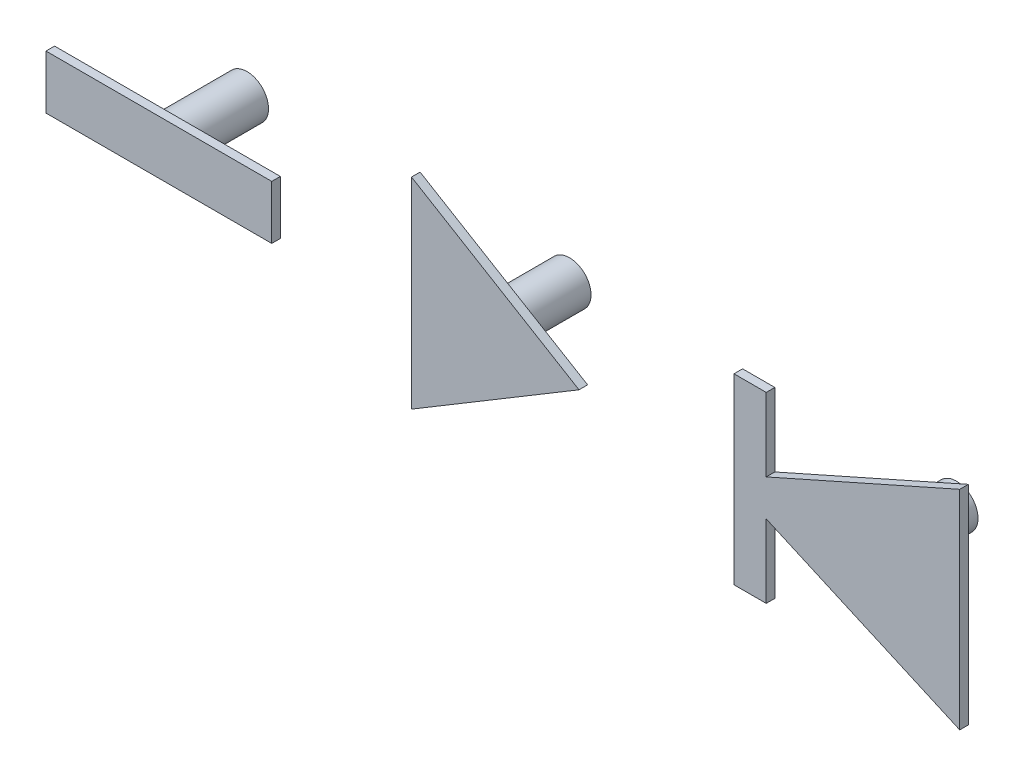
SolidWorks part; units mm, degrees
ref_plane "Front Plane" through (0, 0, 0) normal (0, 0, 1) x (1, 0, 0)
ref_plane "Top Plane" through (0, 0, 0) normal (0, 1, 0) x (1, 0, 0)
ref_plane "Right Plane" through (0, 0, 0) normal (1, 0, 0) x (0, 0, -1)
sketch "Sketch2" plane through (0, 0, 0) normal (0, 0, 1) x (1, 0, 0)
  line L0 (-5, 5.1169) -> (-5, -5.1169)
  line L1 (-4.2428, -5.5457) -> (4.2854, -0.4287)
  line L2 (4.2854, 0.4287) -> (-4.2428, 5.5457)
  line L3 (10, 4.5) -> (10, -4.5)
  line L4 (10.5, -5) -> (12.5, -5)
  line L5 (13, -4.5) -> (13, -2)
  line L6 (13, -2) -> (21.2969, -5.6875)
  line L7 (22, -5.2306) -> (22, 5.2306)
  line L8 (21.2969, 5.6875) -> (13, 2)
  line L9 (13, 2) -> (13, 4.5)
  line L10 (12.5, 5) -> (10.5, 5)
  line L12 (-21.5, 2) -> (-10.5, 2)
  line L13 (-22, 1.5) -> (-22, -1.5)
  line L14 (-21.5, -2) -> (-10.5, -2)
  line L15 (-10, 1.5) -> (-10, -1.5)
  arc A0 (21.2969, 5.6875) -> (22, 5.2306) centre (21.5, 5.2306) cw
  arc A1 (22, -5.2306) -> (21.2969, -5.6875) centre (21.5, -5.2306) cw
  arc A2 (12.5, -5) -> (13, -4.5) centre (12.5, -4.5) ccw
  arc A3 (10.5, -5) -> (10, -4.5) centre (10.5, -4.5) cw
  arc A4 (13, 4.5) -> (12.5, 5) centre (12.5, 4.5) ccw
  arc A5 (10, 4.5) -> (10.5, 5) centre (10.5, 4.5) cw
  arc A6 (4.2854, -0.4287) -> (4.2854, 0.4287) centre (4.0282, 0) ccw
  arc A7 (-4.2428, -5.5457) -> (-5, -5.1169) centre (-4.5, -5.1169) cw
  arc A8 (-4.2428, 5.5457) -> (-5, 5.1169) centre (-4.5, 5.1169) ccw
  arc A9 (-10.5, 2) -> (-10, 1.5) centre (-10.5, 1.5) cw
  arc A10 (-10.5, -2) -> (-10, -1.5) centre (-10.5, -1.5) ccw
  arc A11 (-22, -1.5) -> (-21.5, -2) centre (-21.5, -1.5) ccw
  arc A12 (-22, 1.5) -> (-21.5, 2) centre (-21.5, 1.5) cw
  dimension "D1" = 0.5
sketch "Sketch3" plane through (0, 0, 0) normal (0, 0, 1) x (1, 0, 0)
  line L1 (-24, 10) -> (25, 10)
  line L2 (-25, 9) -> (-25, -9)
  line L3 (-24, -10) -> (25, -10)
  line L4 (26, 9) -> (26, -9)
  arc A0 (25, 10) -> (26, 9) centre (25, 9) cw
  arc A1 (26, -9) -> (25, -10) centre (25, -9) cw
  arc A2 (-24, -10) -> (-25, -9) centre (-24, -9) cw
  arc A3 (-24, 10) -> (-25, 9) centre (-24, 9) ccw
  dimension "D1" = 1
ref_plane "Plane1" through (0, 0, 5) normal (0, 0, 1) x (1, 0, 0)
sketch "Sketch4" plane through (0, 0, 5) normal (0, 0, 1) x (1, 0, 0)
  line L0 (-5, 5.1169) -> (-5, -5.1169)
  line L1 (-4.2428, -5.5457) -> (4.2854, -0.4287)
  line L2 (4.2854, 0.4287) -> (-4.2428, 5.5457)
  line L3 (10, 4.5) -> (10, -4.5)
  line L4 (10.5, -5) -> (12.5, -5)
  line L5 (13, -4.5) -> (13, -2)
  line L6 (13, -2) -> (21.2969, -5.6875)
  line L7 (22, -5.2306) -> (22, 5.2306)
  line L8 (21.2969, 5.6875) -> (13, 2)
  line L9 (13, 2) -> (13, 4.5)
  line L10 (12.5, 5) -> (10.5, 5)
  line L12 (-21.5, 2) -> (-10.5, 2)
  line L13 (-22, 1.5) -> (-22, -1.5)
  line L14 (-21.5, -2) -> (-10.5, -2)
  line L15 (-10, 1.5) -> (-10, -1.5)
  arc A0 (21.2969, 5.6875) -> (22, 5.2306) centre (21.5, 5.2306) cw
  arc A1 (22, -5.2306) -> (21.2969, -5.6875) centre (21.5, -5.2306) cw
  arc A2 (12.5, -5) -> (13, -4.5) centre (12.5, -4.5) ccw
  arc A3 (10.5, -5) -> (10, -4.5) centre (10.5, -4.5) cw
  arc A4 (13, 4.5) -> (12.5, 5) centre (12.5, 4.5) ccw
  arc A5 (10, 4.5) -> (10.5, 5) centre (10.5, 4.5) cw
  arc A6 (4.2854, -0.4287) -> (4.2854, 0.4287) centre (4.0282, 0) ccw
  arc A7 (-4.2428, -5.5457) -> (-5, -5.1169) centre (-4.5, -5.1169) cw
  arc A8 (-4.2428, 5.5457) -> (-5, 5.1169) centre (-4.5, 5.1169) ccw
  arc A9 (-10.5, 2) -> (-10, 1.5) centre (-10.5, 1.5) cw
  arc A10 (-10.5, -2) -> (-10, -1.5) centre (-10.5, -1.5) ccw
  arc A11 (-22, -1.5) -> (-21.5, -2) centre (-21.5, -1.5) ccw
  arc A12 (-22, 1.5) -> (-21.5, 2) centre (-21.5, 1.5) cw
  dimension "D1" = 0.5
sketch "Sketch5" plane through (0, 0, 5) normal (0, 0, 1) x (1, 0, 0)
  line L0 (-4.25, 4.6754) -> (-4.25, -4.6754)
  line L1 (-4.25, -4.6754) -> (3.5423, 0)
  line L2 (3.5423, 0) -> (-4.25, 4.6754)
  line L3 (10.75, 4.25) -> (10.75, -4.25)
  line L4 (10.75, -4.25) -> (12.25, -4.25)
  line L5 (12.25, -4.25) -> (12.25, -0.8459)
  line L6 (12.25, -0.8459) -> (21.25, -4.8459)
  line L7 (21.25, -4.8459) -> (21.25, 4.8459)
  line L8 (21.25, 4.8459) -> (12.25, 0.8459)
  line L9 (12.25, 0.8459) -> (12.25, 4.25)
  line L10 (12.25, 4.25) -> (10.75, 4.25)
  line L12 (-21.25, 1.25) -> (-10.75, 1.25)
  line L13 (-10.75, 1.25) -> (-10.75, -1.25)
  line L14 (-21.25, -1.25) -> (-10.75, -1.25)
  line L15 (-21.25, 1.25) -> (-21.25, -1.25)
extrude "Boss-Extrude3" add sketch "Sketch5" along normal blind 0.1 and the other way blind 0.3
sketch "Sketch6" plane through (0, 0, 5) normal (0, 0, 1) x (1, 0, 0)
  circle A0 centre (-16, 0) radius 1
  circle A1 centre (-1, 0) radius 1
  circle A2 centre (17, 0) radius 1
extrude "Boss-Extrude4" add sketch "Sketch6" against normal blind 4
